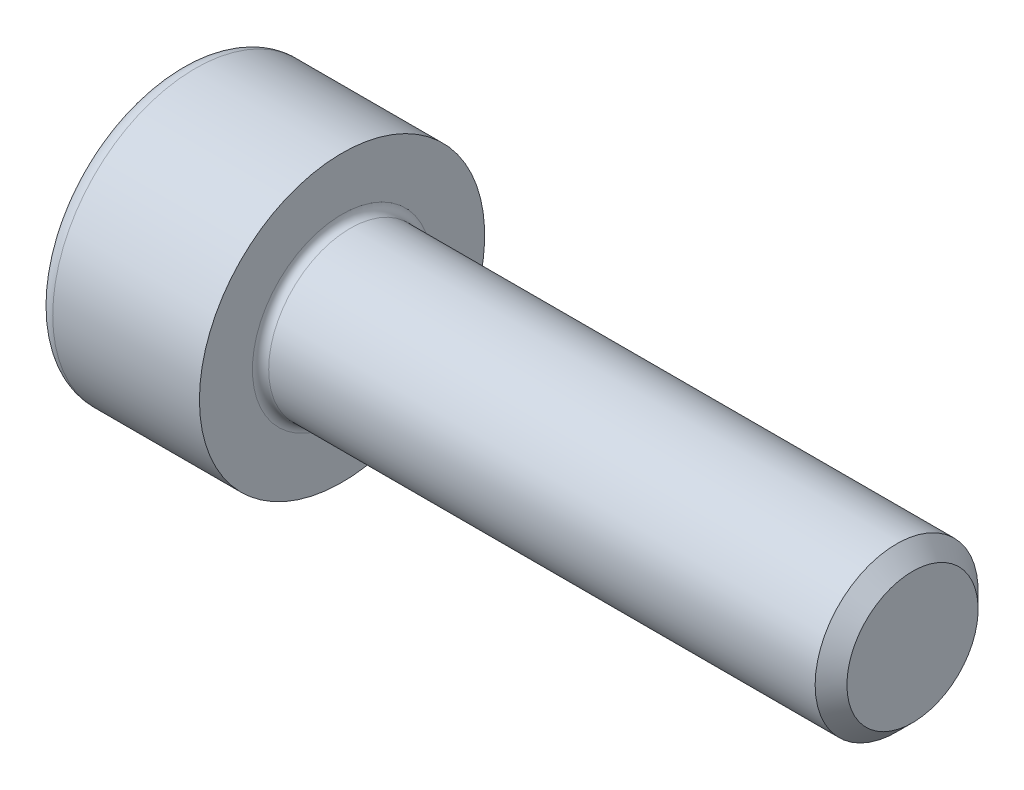
SolidWorks part; units mm, degrees
revolve "Base-Revolve" add sketch "BodySke"
sketch "BodySke" plane through (0, 0, 0) normal (0, 0, 1) x (1, 0, 0)
  line L0 (0, 0) -> (0, 3.5)
  line L1 (0, 3.5) -> (4, 3.5)
  line L2 (4, 3.5) -> (4, 2)
  line L3 (4, 2) -> (17.61, 2)
  line L4 (18, 1.61) -> (18, 0)
  line L5 (18, 0) -> (0, 0)
  line L6 (-31.75, 0) -> (127, 0) construction
  line L8 (18, 1.61) -> (17.61, 2)
  line L10 (18, -1.61) -> (17.61, -2) construction
  line L11 (4.7, 9.525) -> (4.7, 3.175) construction
  line L12 (8, 9.525) -> (8, 3.175) construction
  line L13 (2.0069, 9.525) -> (2.0069, 3.175) construction
  dimension "Head_ht" = 4
  dimension "Length" = 14
  dimension "Body_ch_ang" = 45
  dimension "Diameter" = 4
  dimension "Minor_dia" = 3.22
  dimension "Advance" = 0.7
  dimension "Thread_nom" = 10
  dimension "Thread_length" = 15.9931
  dimension "Head_dia" = 7
cosmetic thread "ThreadCosmetic" [suppressed]
fillet "Fillet1" radius 0.2 1 edges at (4, 0, 2)
fillet "Fillet2" radius 0.4 1 edges at (0, 0, 3.5)
ref_plane "Plane1" through (0, 0, 0) normal (0, 0, 1) x (1, 0, 0)
ref_plane "Plane2" through (0, 0, 0) normal (0, 1, 0) x (1, 0, 0)
ref_plane "Plane3" through (0, 0, 0) normal (1, 0, 0) x (0, 0, -1)
sketch "Sketch2" plane through (0, 0, 0) normal (0, 0, 1) x (1, 0, 0)
  line L0 (0, 1.51) -> (2, 1.51)
  line L1 (2, 1.51) -> (2.8718, 0)
  line L2 (-31.75, 0) -> (127, 0) construction
  line L3 (2.8718, 0) -> (0, 0)
  line L4 (0, 0) -> (0, 1.51)
  line L6 (0, 0) -> (47.625, 0) construction
  dimension "D1" = 1.51
  dimension "D2" = 60
  dimension "Depth" = 2
revolve "Hex-PreBroach" cut sketch "Sketch2" angle 360 about L6
sketch "Sketch3" plane through (0, 0, 0) normal (-1, 0, 0) x (0, 0.5, 0.866)
  line L0 (0.8718, 1.51) -> (-0.8718, 1.51)
  line L1 (-0.8718, 1.51) -> (-1.7436, 0)
  line L2 (0.8718, 1.51) -> (1.7436, 0)
  line L3 (0.8718, -1.51) -> (1.7436, 0)
  line L4 (0.8718, -1.51) -> (-0.8718, -1.51)
  line L5 (-0.8718, -1.51) -> (-1.7436, 0)
  dimension "D1" = 1.51
  dimension "D2" = 1.51
  dimension "Hex_size" = 3.02
extrude "Hex" cut sketch "Sketch3" against normal blind 2
sketch "ThdSchSke" plane through (0, 0, 0) normal (0, 0, 1) x (1, 0, 0)
  line L0 (9, -1.61) -> (8.7269, -2)
  line L1 (9, -1.61) -> (9.2731, -2)
  line L2 (9.2731, -2) -> (9.2731, -2.5)
  line L3 (-3.175, 0) -> (5.1513, 0) construction
  line L4 (0, 3.1) -> (0, -3.1) construction
  line L5 (9.2731, -2.5) -> (8.7269, -2.5)
  line L6 (8.7269, -2.5) -> (8.7269, -2)
  dimension "Thread_minor" = 3.22
  dimension "Diameter" = 4
  dimension "Start" = 9
revolve "ThreadSchematic" [suppressed] cut sketch "ThdSchSke" angle 360 about L3
pattern_linear "ThdSchPat" [suppressed]
equation "\"D2@Sketch3\" = \"Hex_size@Sketch3\" / 2"
equation "\"D1@Sketch3\" = \"Hex_size@Sketch3\" / 2"
equation "\"D1@Sketch2\" = \"Hex_size@Sketch3\" / 2"
equation "\"Thread_minor@ThreadCosmetic\"  =  \"Minor_dia@BodySke\""
equation "\"Depth@Sketch2\" =  \"Key_eng@Hex\""
equation "\"Thread_length@ThreadCosmetic\" = ((sgn( (\"Length@BodySke\" - \"Advance@BodySke\" * 3.0) - \"Thread_nom@BodySke\" )-1)*( (\"Length@BodySke\" - \"Advance@BodySke\" * 3.0) - \"Thread_nom@BodySke\" ))/-2+ \"Thread_nom@BodySke\""
equation "\"Thread_minor@ThdSchSke\" = \"Minor_dia@BodySke\""
equation "\"Diameter@ThdSchSke\" = \"Diameter@BodySke\""
equation "\"Overcut@ThdSchSke\" = \"Diameter@BodySke\" * 1.25"
equation "\"Start@ThdSchSke\" = \"Head_ht@BodySke\" + \"Length@BodySke\" - \"Thread_length@ThreadCosmetic\"  '---Non-countersunk---"
equation "\"Num_threads@ThdSchPat\" = int( \"Thread_length@ThreadCosmetic\" / \"Advance@BodySke\" + 0.999 )  + 1"
equation "\"Advance@ThdSchPat\" = \"Thread_length@ThreadCosmetic\" /  (\"Num_threads@ThdSchPat\" - 1) 'relax it"
equation "\"Num_threads@ThdSchPat\" = \"Num_threads@ThdSchPat\" - sgn( \"Num_threads@ThdSchPat\" - 1) '---chamfered tips only---"
